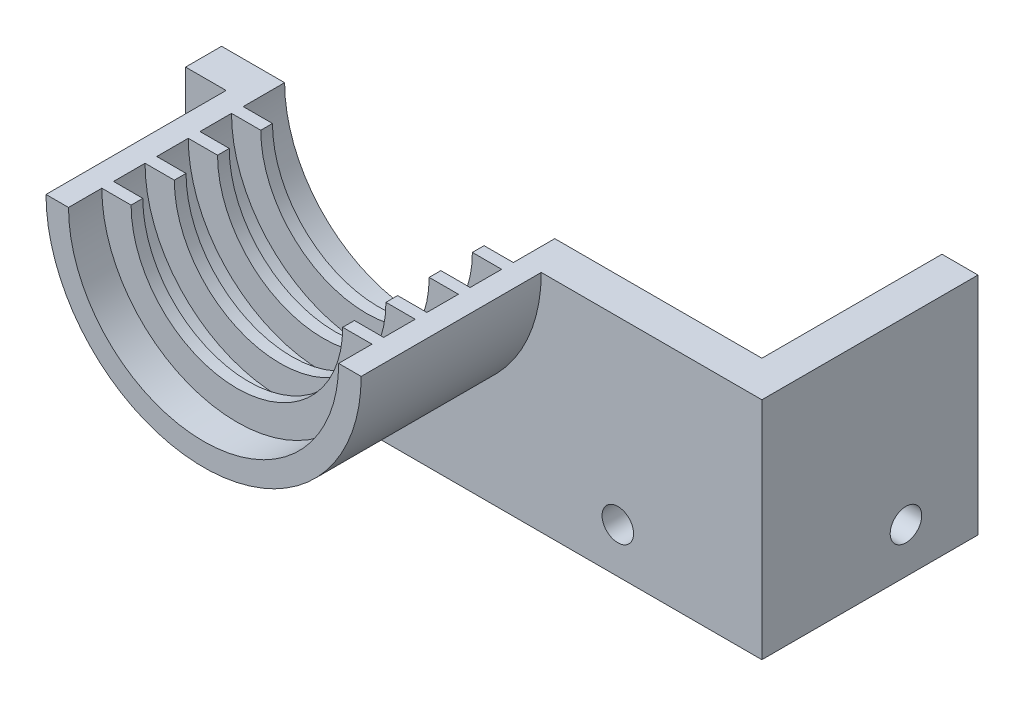
SolidWorks part; units mm, degrees
ref_plane "Front Plane" through (0, 0, 0) normal (0, 0, 1) x (1, 0, 0)
ref_plane "Top Plane" through (0, 0, 0) normal (0, 1, 0) x (1, 0, 0)
ref_plane "Right Plane" through (0, 0, 0) normal (1, 0, 0) x (0, 0, -1)
sketch "Sketch1" plane through (0, 0, 0) normal (0, 0, 1) x (1, 0, 0)
  line L1 (0, 0) -> (66, 0)
  line L2 (0, 0) -> (0, 33)
  line L3 (0, 33) -> (66, 33)
  line L4 (66, 0) -> (66, 33)
  dimension "D1" = 66
  dimension "D2" = 33
extrude "Boss-Extrude1" add sketch "Sketch1" along normal blind 4
sketch "Sketch2" plane through (0, 0, 4) normal (0, 0, 1) x (1, 0, 0)
  line L0 (66, 33) -> (0, 33) construction
  line L1 (18, 33) -> (48, 33)
  arc A0 (18, 33) -> (48, 33) centre (33, 33) ccw
  dimension "D1" = 30
extrude "Cut-Extrude1" cut sketch "Sketch2" against normal through all
sketch "Sketch3" plane through (0, 0, 4) normal (0, 0, 1) x (1, 0, 0)
  line L0 (18, 33) -> (15.5, 33)
  line L1 (48, 33) -> (50.5, 33)
  line L2 (66, 0) -> (66, 33) construction
  arc A0 (18, 33) -> (48, 33) centre (33, 33) ccw
  arc A1 (18, 33) -> (48, 33) centre (33, 33) ccw construction
  arc A2 (15.5, 33) -> (50.5, 33) centre (33, 33) ccw
  point P1 (0, 0)
  dimension "D1" = 35
  dimension "D2" = 33
extrude "Boss-Extrude2" add sketch "Sketch3" along normal blind 20
ref_plane "Plane1" through (0, 0, 4.6) normal (0, 0, 1) x (1, 0, 0)
ref_plane "Plane2" through (0, 0, 9.2) normal (0, 0, 1) x (1, 0, 0)
ref_plane "Plane3" through (0, 0, 9.4) normal (0, 0, 1) x (1, 0, 0)
ref_plane "Plane4" through (0, 0, 14.2) normal (0, 0, 1) x (1, 0, 0)
ref_plane "Plane5" through (0, 0, 19) normal (0, 0, 1) x (1, 0, 0)
sketch "Sketch5" plane through (0, 0, 4.6) normal (0, 0, 1) x (1, 0, 0)
  line L0 (18, 33) -> (21.25, 33)
  line L1 (44.75, 33) -> (48, 33)
  arc A0 (21.25, 33) -> (44.75, 33) centre (33, 33) ccw
  arc A1 (18, 33) -> (48, 33) centre (33, 33) ccw
  dimension "D1" = 23.5
  dimension "D2" = 30
extrude "Boss-Extrude3" add sketch "Sketch5" along normal blind 1.3
sketch "Sketch6" plane through (0, 0, 9.4) normal (0, 0, 1) x (1, 0, 0)
  line L0 (18, 33) -> (21.25, 33)
  line L1 (44.75, 33) -> (48, 33)
  arc A0 (21.25, 33) -> (44.75, 33) centre (33, 33) ccw
  arc A1 (18, 33) -> (48, 33) centre (33, 33) ccw
  dimension "D1" = 23.5
  dimension "D2" = 30
extrude "Boss-Extrude4" add sketch "Sketch6" along normal blind 1.3
sketch "Sketch7" plane through (0, 0, 14.2) normal (0, 0, 1) x (1, 0, 0)
  line L0 (18, 33) -> (21.25, 33)
  line L1 (44.75, 33) -> (48, 33)
  arc A0 (21.25, 33) -> (44.75, 33) centre (33, 33) ccw
  arc A1 (18, 33) -> (48, 33) centre (33, 33) ccw
  dimension "D1" = 23.5
  dimension "D2" = 30
extrude "Boss-Extrude5" add sketch "Sketch7" along normal blind 1.3
sketch "Sketch8" plane through (0, 0, 19) normal (0, 0, 1) x (1, 0, 0)
  line L0 (18, 33) -> (21.25, 33)
  line L1 (44.75, 33) -> (48, 33)
  arc A0 (21.25, 33) -> (44.75, 33) centre (33, 33) ccw
  arc A1 (18, 33) -> (48, 33) centre (33, 33) ccw
  dimension "D1" = 23.5
  dimension "D2" = 30
extrude "Boss-Extrude6" add sketch "Sketch8" along normal blind 1.3
sketch "Sketch11" plane through (0, 0, 4) normal (0, 0, 1) x (1, 0, 0)
  line L0 (0, 0) -> (66, 0) construction
  line L1 (66, 0) -> (0, 0)
  line L2 (66, 0) -> (66, 8)
  line L3 (66, 8) -> (0, 8)
  line L4 (0, 0) -> (0, 8)
  line L5 (66, 0) -> (66, 33) construction
  line L6 (0, 33) -> (0, 0) construction
  dimension "D1" = 8
extrude "Cut-Extrude4" cut sketch "Sketch11" against normal blind 10
sketch "Sketch13" plane through (0, 0, 0) normal (-1, 0, 0) x (0, 0, 1)
  line L0 (4, 33) -> (4, 8) construction
  line L1 (4, 8) -> (0, 8)
  line L2 (4, 8) -> (4, 33)
  line L3 (4, 33) -> (0, 33)
  line L4 (0, 8) -> (0, 33)
  line L5 (4, 33) -> (0, 33) construction
  line L6 (0, 33) -> (0, 8) construction
  line L7 (0, 8) -> (4, 8) construction
extrude "Boss-Extrude7" add sketch "Sketch13" along normal blind 5
sketch "Sketch14" plane through (66, 0, 0) normal (1, 0, 0) x (0, 0, -1)
  line L0 (0, 8) -> (-4, 8) construction
  line L1 (0, 8) -> (-4, 8)
  line L2 (0, 8) -> (0, 33)
  line L3 (0, 33) -> (-4, 33)
  line L4 (-4, 8) -> (-4, 33)
  line L5 (-4, 33) -> (0, 33) construction
  line L6 (-4, 8) -> (-4, 33) construction
  line L7 (0, 8) -> (0, 33) construction
extrude "Boss-Extrude8" add sketch "Sketch14" along normal blind 8
sketch "Sketch16" plane through (74, 0, 0) normal (1, 0, 0) x (0, 0, -1)
  line L1 (-4, 33) -> (-4, 8) construction
  line L2 (0, 33) -> (-4, 33) construction
  circle A0 centre (14, 13) radius 1.75
  dimension "D1" = 3.5
  dimension "D2" = 18
  dimension "D3" = 20
extrude "Cut-Extrude5" cut sketch "Sketch16" against normal blind 12
sketch "Sketch17" plane through (0, 0, 4) normal (0, 0, 1) x (1, 0, 0)
  line L3 (74, 33) -> (50.5, 33) construction
  line L5 (74, 33) -> (74, 8) construction
  circle A0 centre (59, 13) radius 1.75
  point P2 (59.0229, 12.0861)
  dimension "D1" = 3.5
  dimension "D2" = 20
  dimension "D3" = 15
extrude "Cut-Extrude8" cut sketch "Sketch17" against normal blind 12
sketch "Sketch18" plane through (74, 0, 0) normal (1, 0, 0) x (0, 0, -1)
  line L0 (-4, 33) -> (-4, 8) construction
  line L1 (-4, 33) -> (0, 33)
  line L2 (-4, 33) -> (-4, 8)
  line L3 (-4, 8) -> (0, 8)
  line L4 (0, 33) -> (0, 8)
  line L5 (0, 33) -> (-4, 33) construction
  line L6 (0, 8) -> (0, 33) construction
  line L7 (-4, 8) -> (0, 8) construction
extrude "Cut-Extrude9" cut sketch "Sketch18" against normal blind 3
sketch "Sketch19" plane through (71, 0, 0) normal (1, 0, 0) x (0, 0, -1)
  line L0 (0, 33) -> (-4, 33) construction
  line L1 (-4, 33) -> (0, 33)
  line L2 (-4, 33) -> (-4, 8)
  line L3 (-4, 8) -> (0, 8)
  line L4 (0, 33) -> (0, 8)
  line L5 (0, 8) -> (0, 33) construction
  line L6 (-4, 33) -> (-4, 8) construction
  line L7 (-4, 8) -> (0, 8) construction
extrude "Boss-Extrude10" add sketch "Sketch19" along normal blind 4
sketch "Sketch20" plane through (0, 0, 0) normal (0, 0, -1) x (-1, 0, 0)
  line L0 (-75, 8) -> (-75, 33) construction
  line L1 (-75, 33) -> (-71, 33)
  line L2 (-75, 33) -> (-75, 8)
  line L3 (-75, 8) -> (-71, 8)
  line L4 (-71, 33) -> (-71, 8)
  line L5 (-75, 33) -> (-48, 33) construction
  line L6 (5, 8) -> (-75, 8) construction
  dimension "D1" = 4
extrude "Boss-Extrude11" add sketch "Sketch20" along normal blind 20
sketch "Sketch21" plane through (75, 0, 0) normal (1, 0, 0) x (0, 0, -1)
  line L0 (20, 33) -> (-4, 33) construction
  line L1 (-4, 33) -> (-4, 8) construction
  circle A0 centre (12, 13) radius 1.75
  dimension "D1" = 3.5
  dimension "D2" = 20
  dimension "D3" = 16
extrude "Cut-Extrude10" cut sketch "Sketch21" against normal blind 20
sketch "Sketch22" plane through (0, 0, 4) normal (0, 0, 1) x (1, 0, 0)
  line L0 (15.5, 33) -> (-5, 33) construction
  line L1 (-5, 33) -> (11, 33)
  line L2 (-5, 33) -> (-5, 8)
  line L3 (-5, 8) -> (11, 8)
  line L4 (11, 33) -> (11, 8)
  line L5 (75, 8) -> (-5, 8) construction
  line L6 (-5, 8) -> (-5, 33) construction
  dimension "D1" = 16
extrude "Cut-Extrude11" cut sketch "Sketch22" against normal through all
